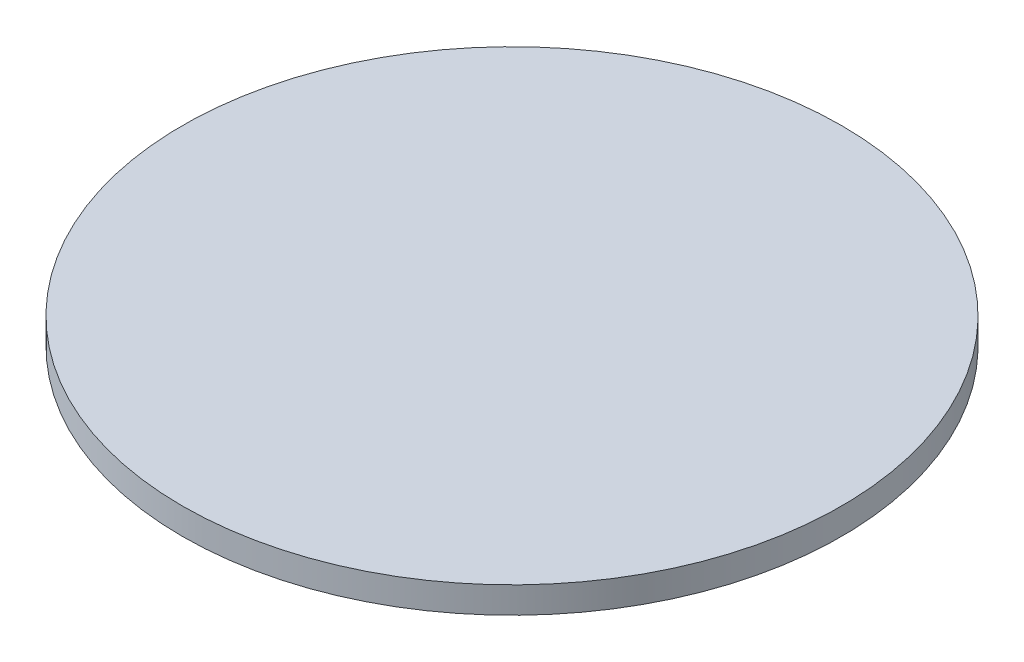
SolidWorks part; units mm, degrees
ref_plane "前视基准面" through (0, 0, 0) normal (0, 0, 1) x (1, 0, 0)
ref_plane "上视基准面" through (0, 0, 0) normal (0, 1, 0) x (1, 0, 0)
ref_plane "右视基准面" through (0, 0, 0) normal (1, 0, 0) x (0, 0, -1)
sketch "草图1" plane through (0, 0, 0) normal (0, 1, 0) x (1, 0, 0)
  circle A0 centre (0, 0) radius 100
  dimension "D1" = 200
extrude "凸台-拉伸1" add sketch "草图1" along normal blind 8
